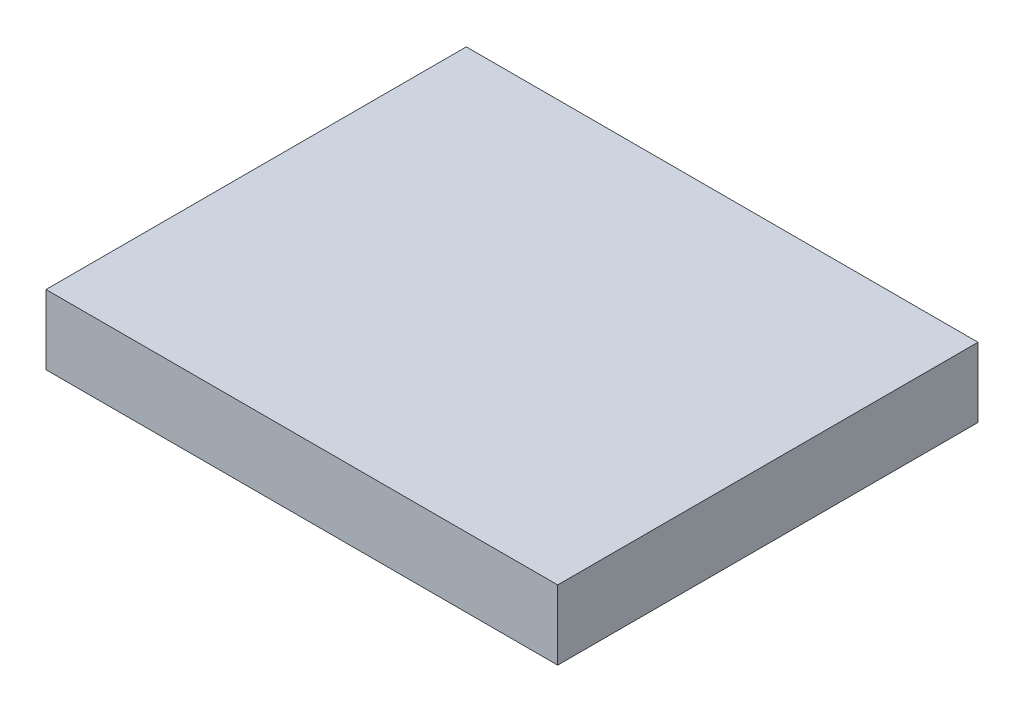
SolidWorks part; units mm, degrees
ref_plane "Front Plane" through (0, 0, 0) normal (0, 0, 1) x (1, 0, 0)
ref_plane "Top Plane" through (0, 0, 0) normal (0, 1, 0) x (1, 0, 0)
ref_plane "Right Plane" through (0, 0, 0) normal (1, 0, 0) x (0, 0, -1)
sketch "Sketch2" plane through (0, 0, 0) normal (0, 1, 0) x (1, 0, 0)
  line L1 (-17.0682, -3.0259) -> (18.4918, -3.0259)
  line L2 (-17.0682, -3.0259) -> (-17.0682, -32.2359)
  line L3 (-17.0682, -32.2359) -> (18.4918, -32.2359)
  line L4 (18.4918, -3.0259) -> (18.4918, -32.2359)
extrude "Boss-Extrude1" add sketch "Sketch2" along normal blind 4.83
